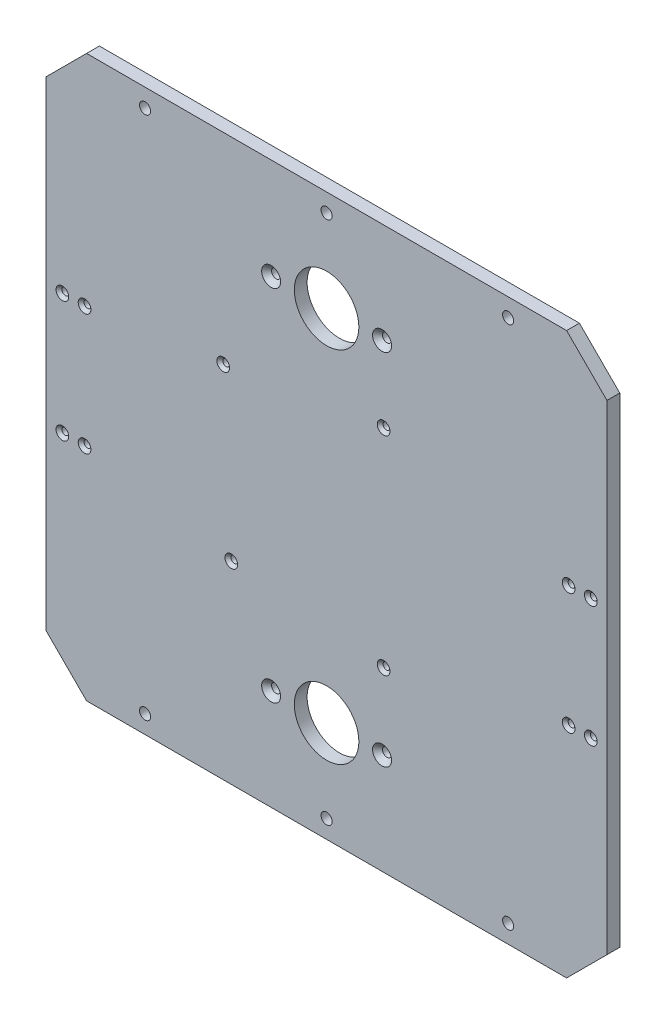
SolidWorks part; units mm, degrees
ref_plane "Front Plane" through (0, 0, 0) normal (0, 0, 1) x (1, 0, 0)
ref_plane "Top Plane" through (0, 0, 0) normal (0, 1, 0) x (1, 0, 0)
ref_plane "Right Plane" through (0, 0, 0) normal (1, 0, 0) x (0, 0, -1)
sketch "Sketch1" plane through (0, 0, 0) normal (0, 0, 1) x (1, 0, 0)
  line L0 (-79.0045, 0) -> (94.053, 0) construction
  line L1 (0, 67.0127) -> (0, -68.6587) construction
  line L3 (139, -139) -> (-139, -139)
  line L4 (139, -139) -> (139, 139)
  line L5 (139, 139) -> (-139, 139)
  line L6 (-139, -139) -> (-139, 139)
  line L7 (139, -139) -> (-139, 139) construction
  line L8 (139, 139) -> (-139, -139) construction
  point P4 (0, 0)
  dimension "D1" = 278
  dimension "D2" = 278
extrude "Boss-Extrude1" add sketch "Sketch1" along normal blind 6.35
chamfer "Chamfer1" distance 20 angle 45 4 edges at (139, -139, 3.175) (139, 139, 3.175) (-139, 139, 3.175) (-139, -139, 3.175)
sketch "Sketch4" plane through (0, 0, 6.35) normal (0, 0, 1) x (1, 0, 0)
  line L0 (0, 186.846) -> (0, -174.5938) construction
  line L1 (219.7737, 0) -> (-232.7917, 0) construction
  line L2 (119, 139) -> (-119, 139) construction
  line L3 (-90, 130) -> (90, 130) construction
  circle A0 centre (-90, 130) radius 2.75
  circle A1 centre (0, 130) radius 2.75
  circle A2 centre (90, 130) radius 2.75
  circle A3 centre (90, -130) radius 2.75
  circle A4 centre (0, -130) radius 2.75
  circle A5 centre (-90, -130) radius 2.75
  dimension "D1" = 5.5
  dimension "D2" = 9
  dimension "D3" = 90
extrude "Cut-Extrude2" cut sketch "Sketch4" against normal blind 76.2
sketch "Sketch8" plane through (0, 0, 6.35) normal (0, 0, 1) x (1, 0, 0)
  line L0 (0, 225.553) -> (0, -227.4564) construction
  line L1 (119, 139) -> (-119, 139) construction
  line L2 (139, 0) -> (-139, 0) construction
  line L3 (139, -119) -> (139, 119) construction
  line L4 (-139, 119) -> (-139, -119) construction
  circle A0 centre (0, 89) radius 16
  circle A1 centre (0, -89) radius 16
  dimension "D3" = 32
  dimension "D1" = 50
extrude "Cut-Extrude4" cut sketch "Sketch8" against normal blind 105
hole_wizard "CSK for M4 Flat Head Machine Screw2" positions "Sketch10" profile "Sketch9" countersink size "M4" standard "ANSI Metric" end condition through all
sketch "Sketch10" plane through (0, 0, 6.35) normal (0, 0, 1) x (1, 0, 0)
  line L5 (0, 205.0159) -> (0, -212.7914) construction
  line L6 (16, 89) -> (-16, 89) construction
  line L8 (156.7583, 0) -> (-175.5166, 0) construction
  line L9 (-16, 89) -> (16, 89) construction
  circle A1 centre (0, 89) radius 16 construction
  point P70 (-27.5, 89)
  point P74 (27.5, 89)
  point P76 (27.5, -89)
  point P77 (-27.5, -89)
  dimension "D3" = 55
sketch "Sketch9" plane through (-27.5, 89, 6.35) normal (1, 0, 0) x (0, -1, 0)
  line L0 (0, 0) -> (0, 6.35)
  line L1 (0, 6.35) -> (2.25, 6.35)
  line L2 (2.25, 6.35) -> (2.25, 2.45)
  line L3 (2.25, 2.45) -> (4.7, 0)
  line L5 (4.7, 0) -> (0, 0)
  line L6 (-2.25, 2.45) -> (-4.7, 0) construction
  line L11 (0, -6.35) -> (0, 107.95) construction
  dimension "Thru Hole Dia." = 4.5
  dimension "Thru Hole Depth" = 6.35
  dimension "Near C'Sink Dia." = 9.4
  dimension "Near C'Sink Angle" = 90
hole_wizard "CSK for M3 Flat Head Machine Screw1" positions "Sketch12" profile "Sketch11" countersink size "M3" standard "ANSI Metric" end condition through all
sketch "Sketch12" plane through (0, 0, 6.35) normal (0, 0, 1) x (1, 0, 0)
  line L0 (0, 139) -> (0, -139) construction
  line L1 (119, 139) -> (-119, 139) construction
  line L2 (-119, -139) -> (119, -139) construction
  line L4 (-139, 0) -> (139, 0) construction
  line L5 (-139, 119) -> (-139, -119) construction
  line L6 (139, -119) -> (139, 119) construction
  point P0 (-131, 30)
  point P2 (-120, 30)
  point P24 (-120, -30)
  point P25 (-131, -30)
  point P26 (131, -30)
  point P27 (120, -30)
  point P28 (120, 30)
  point P29 (131, 30)
  dimension "D1" = 11
  dimension "D2" = 60
  dimension "D3" = 8
sketch "Sketch11" plane through (-131, 30, 6.35) normal (1, 0, 0) x (0, -1, 0)
  line L0 (0, 0) -> (0, 6.35)
  line L1 (0, 6.35) -> (1.7, 6.35)
  line L2 (1.7, 6.35) -> (1.7, 1.45)
  line L3 (1.7, 1.45) -> (3.15, 0)
  line L5 (3.15, 0) -> (0, 0)
  line L6 (-1.7, 1.45) -> (-3.15, 0) construction
  line L11 (0, -6.35) -> (0, 107.95) construction
  dimension "Thru Hole Dia." = 3.4
  dimension "Thru Hole Depth" = 6.35
  dimension "Near C'Sink Dia." = 6.3
  dimension "Near C'Sink Angle" = 90
sketch "Sketch23" plane through (-4.5902, -1.9963, 0) normal (0, 0, -1) x (0, -1, 0)
  point P1 (49.1412, -32.8536)
  point P6 (41.1412, 42.6464)
  point P10 (-41.3588, 46.6464)
  point P14 (-53.8588, -32.8536)
hole_wizard "CSK for M3 Flat Head Machine Screw2" positions "Sketch25" profile "Sketch24" countersink size "M3" standard "ANSI Metric" end condition through all
sketch "Sketch25" plane through (0, 0, 6.35) normal (0, 0, 1) x (1, 0, 0)
  point P0 (-47.2366, -43.1375)
  point P5 (-51.2366, 39.3625)
  point P7 (28.2634, 51.8625)
  point P9 (28.2634, -51.1375)
sketch "Sketch24" plane through (-47.2366, -43.1375, 6.35) normal (1, 0, 0) x (0, -1, 0)
  line L0 (0, 0) -> (0, 6.35)
  line L1 (0, 6.35) -> (1.7, 6.35)
  line L2 (1.7, 6.35) -> (1.7, 1.45)
  line L3 (1.7, 1.45) -> (3.15, 0)
  line L5 (3.15, 0) -> (0, 0)
  line L6 (-1.7, 1.45) -> (-3.15, 0) construction
  line L11 (0, -6.35) -> (0, 107.95) construction
  dimension "Thru Hole Dia." = 3.4
  dimension "Thru Hole Depth" = 6.35
  dimension "Near C'Sink Dia." = 6.3
  dimension "Near C'Sink Angle" = 90
equation "\"plate_thickness\"= 6.35 'thickness of the plate "
equation "\"height\"= 180"
equation "\"D1@Boss-Extrude1\"=\"plate_thickness\""
equation "\"t_height\"= 200"
equation "\"t_width\"= 240"
equation "\"t_length\"= 240"
equation "\"plate_spacing\"= 1"
equation "\"front_plate_height\"= \"t_height\" + 38"
equation "\"front_plate_width\"= \"t_width\" + 38"
equation "\"side_plate_height\"= \"front_plate_height\""
equation "\"side_plate_length\"= \"t_length\" + 38"
equation "\"top_plate_width\"= \"front_plate_width\""
equation "\"top_plate_length\"= \"side_plate_length\""
equation "\"D2@Sketch1\"=\"top_plate_width\""
equation "\"D1@Sketch1\"=\"top_plate_length\""
equation "\"plate_hole_spacing\"= 9"
equation "\"connector_D1\"= 70 'the big holes diameter"
equation "\"connector_mtg_D2\"= 5.5 'mounting holes"
equation "\"mtg_dfc\"= 40 'mounting hole distance from center"
equation "\"mtg_hole_D\"= 5.5 'mounting holes"
equation "\"plate_hole_from_edge\"= 9"
equation "\"D1@Sketch4\"=\"mtg_hole_D\""
equation "\"D2@Sketch4\"=\"plate_hole_from_edge\""
equation "\"itx_support_t_slot_length\"= \"t_width\" + (2 * 20.5)"
equation "\"locomotion_length\"= \"t_length\""
equation "\"locomotion_width\"= \"t_width\""
equation "\"locomotion_height\"= 40"
equation "\"itx_mtg_hole_spacing\"= 40"
equation "\"emg30_bracket_hole_len\"= 60"
equation "\"emg30_bracket_hole_wid\"= 11"
equation "\"D2@Sketch12\"=\"emg30_bracket_hole_len\""
equation "\"D1@Sketch12\"=\"emg30_bracket_hole_wid\""
